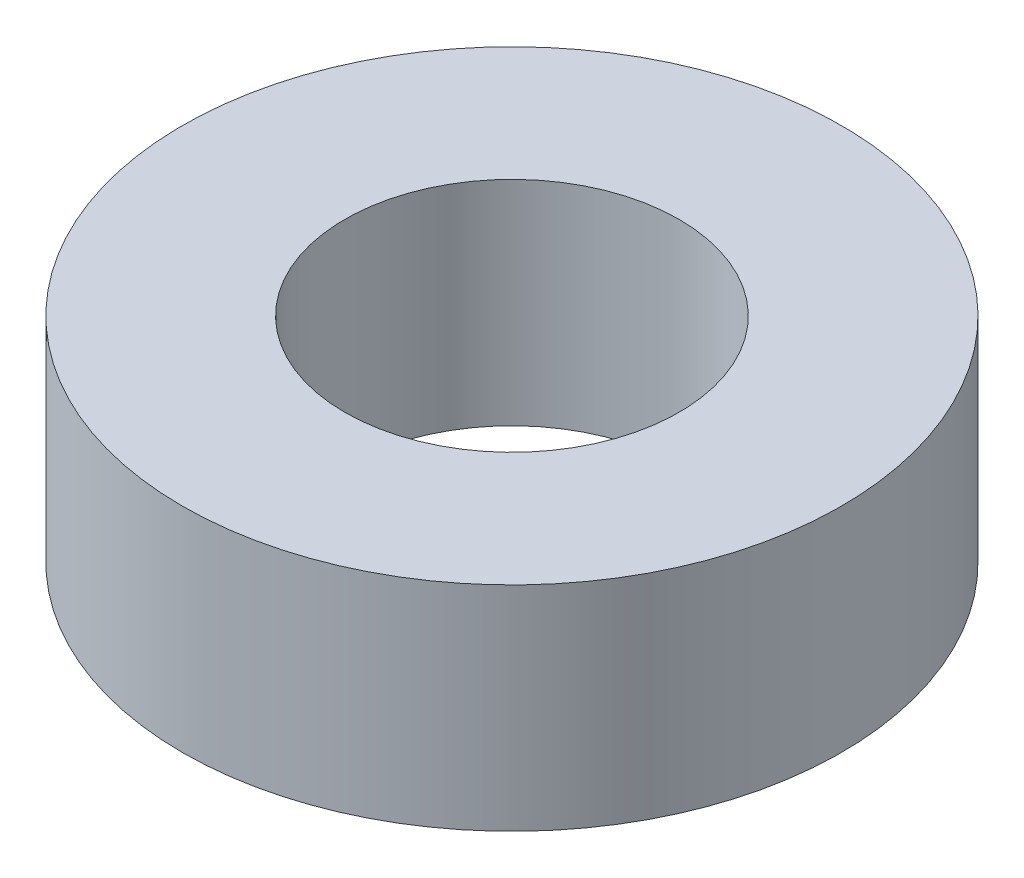
SolidWorks part; units mm, degrees
ref_plane "Plan de face" through (0, 0, 0) normal (0, 0, 1) x (1, 0, 0)
ref_plane "Plan de dessus" through (0, 0, 0) normal (0, 1, 0) x (1, 0, 0)
ref_plane "Plan de droite" through (0, 0, 0) normal (1, 0, 0) x (0, 0, -1)
sketch "Esquisse1" plane through (0, 0, 0) normal (0, 1, 0) x (1, 0, 0)
  circle A0 centre (0, 0) radius 13.9
  circle A1 centre (0, 0) radius 7.05
extrude "Boss.-Extru.1" add sketch "Esquisse1" along normal blind 9
